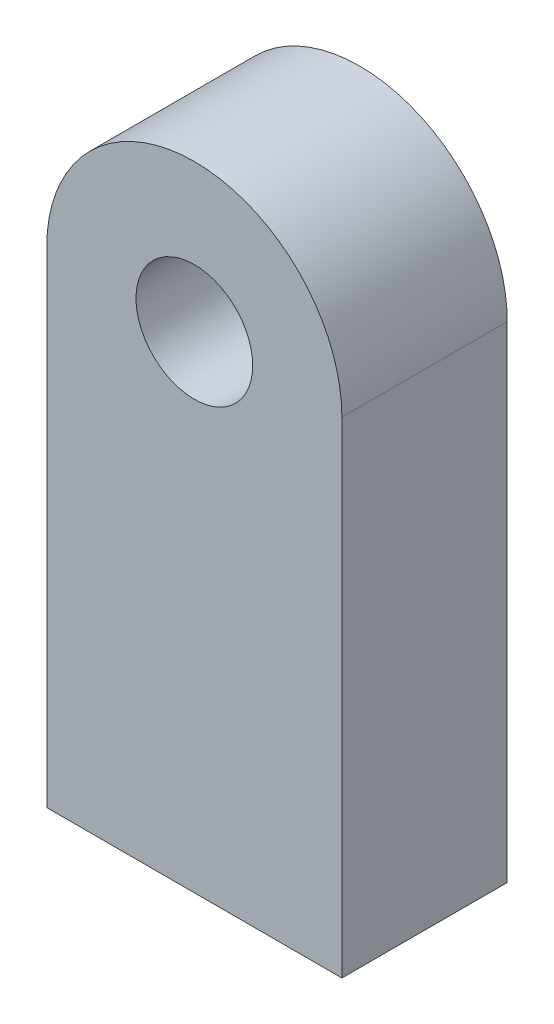
SolidWorks part; units mm, degrees
ref_plane "Front Plane" through (0, 0, 0) normal (0, 0, 1) x (1, 0, 0)
ref_plane "Top Plane" through (0, 0, 0) normal (0, 1, 0) x (1, 0, 0)
ref_plane "Right Plane" through (0, 0, 0) normal (1, 0, 0) x (0, 0, -1)
sketch "Sketch1" plane through (0, 0, 0) normal (0, 0, 1) x (1, 0, 0)
  line L2 (-8.0328, 13.2199) -> (-8.0328, -13.2199)
  line L3 (-8.0328, -13.2199) -> (8.0328, -13.2199)
  line L4 (8.0328, 13.2199) -> (8.0328, -13.2199)
  arc A0 (8.0328, 13.2199) -> (0, 21.2527) centre (0, 13.2199) ccw
  arc A1 (0, 21.2527) -> (-8.0328, 13.2199) centre (0, 13.2199) ccw
  circle A2 centre (0, 13.2199) radius 3.175
  point P0 (0, 0)
  dimension "D1" = 6.35
extrude "Boss-Extrude1" add sketch "Sketch1" along normal blind 9
